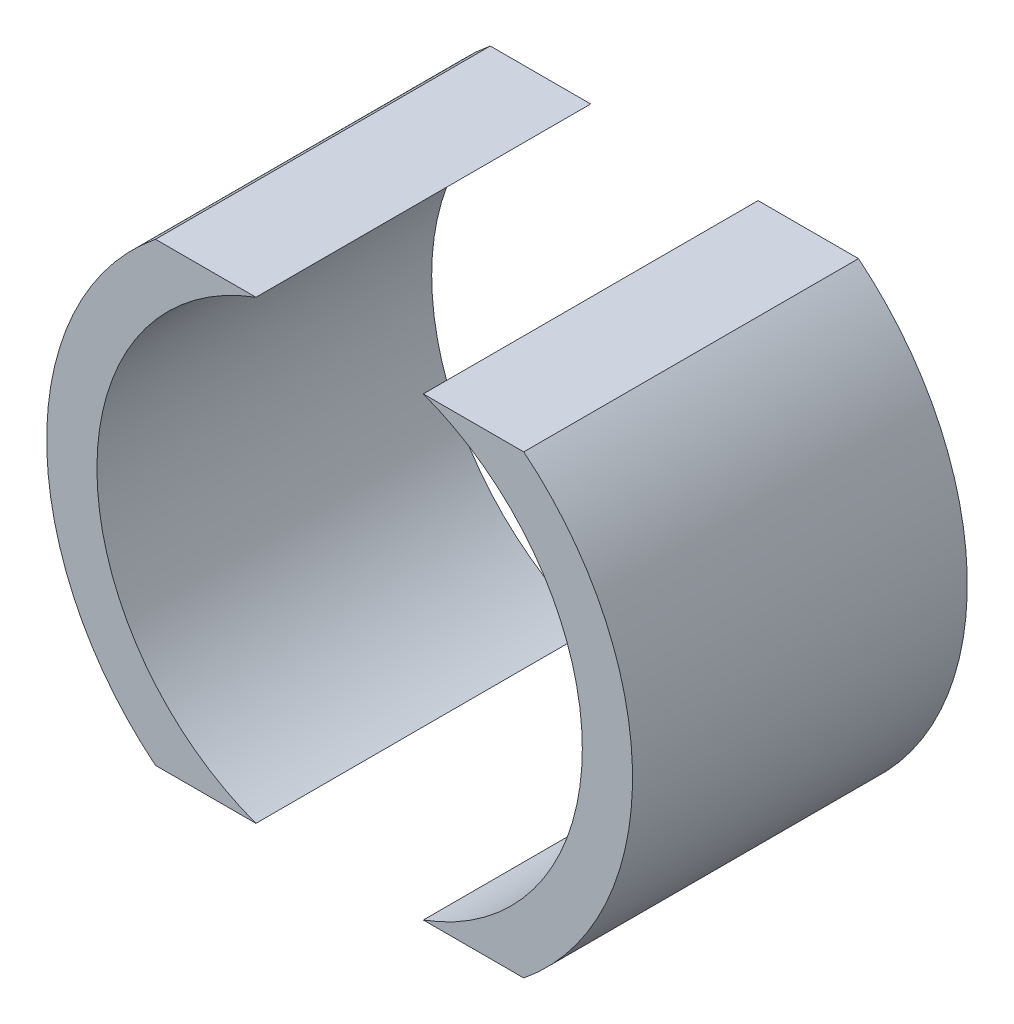
SolidWorks part; units mm, degrees
ref_plane "Front Plane" through (0, 0, 0) normal (0, 0, 1) x (1, 0, 0)
ref_plane "Top Plane" through (0, 0, 0) normal (0, 1, 0) x (1, 0, 0)
ref_plane "Right Plane" through (0, 0, 0) normal (1, 0, 0) x (0, 0, -1)
sketch "Sketch1" plane through (0, 0, 0) normal (0, 0, 1) x (1, 0, 0)
  line L12 (0, 0) -> (-5, 0) construction
  line L13 (-5, 0) -> (-5, 13.6107) construction
  line L14 (0, 0) -> (5, 0) construction
  line L15 (5, 0) -> (5, 13.6107) construction
  line L16 (5, 0) -> (5, -13.6107) construction
  line L17 (-5, 0) -> (-5, -13.6107) construction
  line L18 (-5, 13.6107) -> (-11, 13.6107)
  line L19 (5, 13.6107) -> (11, 13.6107)
  line L20 (5, -13.6107) -> (11, -13.6107)
  line L21 (-5, -13.6107) -> (-11, -13.6107)
  arc A8 (11, -13.6107) -> (11, 13.6107) centre (0, 0) ccw
  arc A9 (5, -13.6107) -> (5, 13.6107) centre (0, 0) ccw
  arc A10 (-5, 13.6107) -> (-5, -13.6107) centre (0, 0) ccw
  arc A11 (-11, 13.6107) -> (-11, -13.6107) centre (0, 0) ccw
  dimension "D1" = 29
  dimension "D2" = 35
  dimension "D3" = 5
  dimension "D4" = 5
extrude "Boss-Extrude3" add sketch "Sketch1" along normal blind 20
